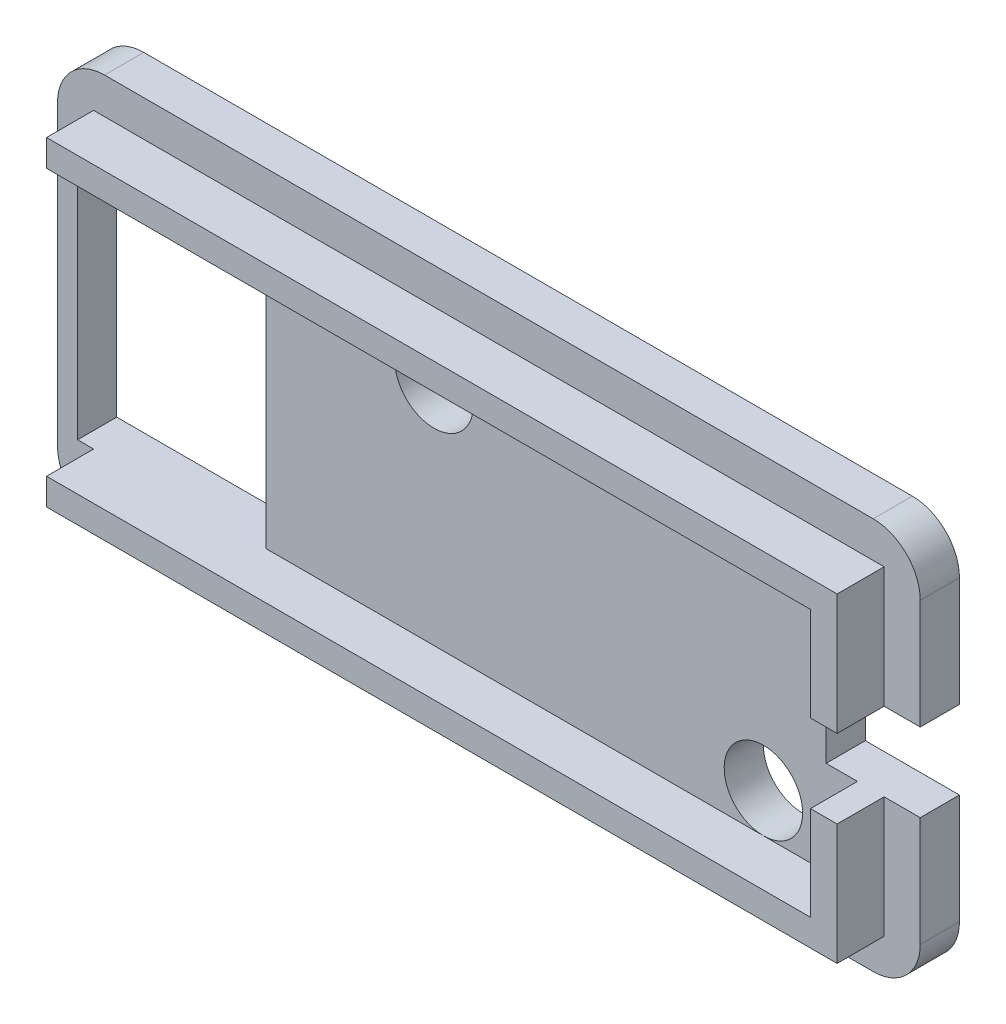
SolidWorks part; units mm, degrees
ref_plane "Alzado" through (0, 0, 0) normal (0, 0, 1) x (1, 0, 0)
ref_plane "Planta" through (0, 0, 0) normal (0, 1, 0) x (1, 0, 0)
ref_plane "Vista lateral" through (0, 0, 0) normal (1, 0, 0) x (0, 0, -1)
sketch "Croquis1" plane through (0, 0, 0) normal (0, 0, 1) x (1, 0, 0)
  line L0 (-27.5, 0) -> (27.5, 0) construction
  line L1 (-27.5, 12.5) -> (27.5, 12.5)
  line L2 (-27.5, 12.5) -> (-27.5, -12.5)
  line L3 (-27.5, -12.5) -> (27.5, -12.5)
  line L4 (27.5, 12.5) -> (27.5, -12.5)
  line L5 (-27.5, 12.5) -> (27.5, -12.5) construction
  line L6 (-27.5, -12.5) -> (27.5, 12.5) construction
  circle A0 centre (-10, 0) radius 2.75
  circle A1 centre (11.5, 0) radius 2.75
  point P0 (0, 0)
  point P12 (0, 0)
  dimension "D3" = 5.5
  dimension "D4" = 17.5
  dimension "D5" = 16
  dimension "D1" = 25
  dimension "D2" = 55
extrude "Saliente-Extruir1" add sketch "Croquis1" along normal blind 2.5 contours L2 L1 L4 L3
sketch "Croquis7" plane through (0, 0, 2.5) normal (0, 0, 1) x (1, 0, 0)
  line L0 (-23.5, 8.5) -> (-23.5, -8.5)
  line L1 (-25.5, 10.5) -> (25.5, 10.5)
  line L2 (-25.5, 10.5) -> (-25.5, -10.5)
  line L3 (-25.5, -10.5) -> (25.5, -10.5)
  line L4 (25.5, 10.5) -> (25.5, -10.5)
  line L5 (-25.5, 10.5) -> (25.5, -10.5) construction
  line L6 (-25.5, -10.5) -> (25.5, 10.5) construction
  line L7 (-23.5, -8.5) -> (23.5, -8.5)
  line L8 (23.5, 8.5) -> (23.5, -8.5)
  line L9 (-23.5, 8.5) -> (23.5, 8.5)
  point P0 (0, 0)
  dimension "D1" = 21
  dimension "D2" = 51
  dimension "D3" = 2
extrude "Saliente-Extruir4" add sketch "Croquis7" along normal blind 3 contours L2 L1 L4 L3 | L0 L7 L8 L9
fillet "Redondeo2" radius 3 4 edges at (-27.5, 12.5, 1.25) (-27.5, -12.5, 1.25) (27.5, -12.5, 1.25) (27.5, 12.5, 1.25)
sketch "Croquis8" plane through (0, 0, 2.5) normal (0, 0, 1) x (1, 0, 0)
  line L1 (-26.225, -8.5) -> (-14.225, -8.5)
  line L2 (-26.225, -8.5) -> (-26.225, 8.5)
  line L3 (-26.225, 8.5) -> (-14.225, 8.5)
  line L4 (-14.225, -8.5) -> (-14.225, 8.5)
  line L5 (-23.5, 8.5) -> (23.5, 8.5) construction
  dimension "D1" = 12
extrude "Cortar-Extruir5" cut sketch "Croquis8" against normal blind 8 and the other way blind 11
sketch "Croquis9" plane through (0, 0, 0) normal (0, 0, -1) x (-1, 0, 0)
  line L0 (0, 0) -> (-27.5, 0) construction
  line L1 (-27.5, 9.5) -> (-27.5, -9.5) construction
  line L3 (-21.5, -2.5) -> (-27.5, -2.5)
  line L4 (-21.5, -2.5) -> (-21.5, 2.5)
  line L5 (-21.5, 2.5) -> (-27.5, 2.5)
  line L6 (-27.5, -2.5) -> (-27.5, 2.5)
  line L7 (-21.5, -2.5) -> (-27.5, 2.5) construction
  line L8 (-21.5, 2.5) -> (-27.5, -2.5) construction
  point P5 (-24.5, 0)
  dimension "D1" = 5
  dimension "D2" = 6
extrude "Cortar-Extruir6" cut sketch "Croquis9" against normal blind 8
sketch "Croquis11" plane through (0, 0, 2.5) normal (0, 0, 1) x (1, 0, 0)
  line L0 (23.5, 8.5) -> (23.5, 2.5) construction
  line L1 (-25.5, 8.5) -> (23.5, 8.5) construction
  line L2 (-25.5, -8.5) -> (23.5, -8.5) construction
  line L3 (23.5, -2.5) -> (23.5, -8.5) construction
  circle A0 centre (-3.5, 6) radius 2.5
  circle A1 centre (17.5, -6) radius 2.5
  dimension "D1" = 5
  dimension "D3" = 2.5
  dimension "D4" = 2.5
  dimension "D5" = 27
  dimension "D2" = 6
extrude "Cortar-Extruir8" cut sketch "Croquis11" against normal through all
sketch "Croquis12" plane through (0, 0, 5.5) normal (0, 0, 1) x (1, 0, 0)
  line L0 (25.5, -10.5) -> (25.5, -10.2) construction
  line L1 (25.5, -2.5) -> (25.5, -10.5) construction
  line L2 (25.5, -10.2) -> (25.2, -10.2) construction
  line L3 (25.2, -10.2) -> (25.2, -10.5) construction
  line L4 (-25.5, -10.5) -> (25.5, -10.5) construction
  line L5 (-25.5, 10.5) -> (-25.5, 10.2) construction
  line L7 (-25.5, 10.5) -> (-25.5, 8.5) construction
  line L8 (-25.5, 10.2) -> (-25.2, 10.2) construction
  line L9 (-25.2, 10.2) -> (-25.2, 10.5) construction
  line L10 (-25.2, 10.2) -> (25.2, 10.2)
  line L11 (-25.2, 10.2) -> (-25.2, -10.2)
  line L12 (-25.2, -10.2) -> (25.2, -10.2)
  line L13 (25.2, 10.2) -> (25.2, -10.2)
  line L14 (-25.5, 10.5) -> (25.5, 10.5) construction
  line L16 (25.5, -10.5) -> (-25.5, -10.5)
  line L17 (25.5, -10.5) -> (25.5, 10.5)
  line L18 (25.5, 10.5) -> (-25.5, 10.5)
  line L19 (-25.5, -10.5) -> (-25.5, 10.5)
extrude "Cortar-Extruir11" cut sketch "Croquis12" against normal blind 3
